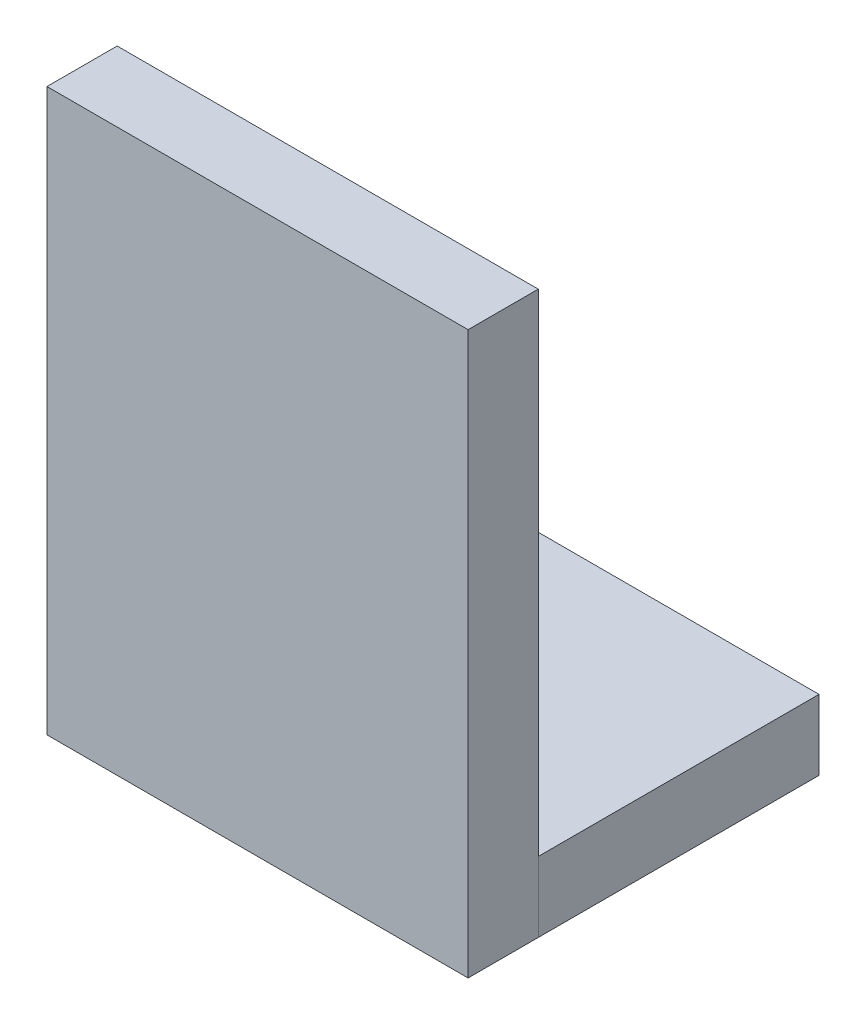
SolidWorks part; units mm, degrees
material "Rubber"
ref_plane "Front Plane" through (0, 0, 0) normal (0, 0, 1) x (1, 0, 0)
ref_plane "Top Plane" through (0, 0, 0) normal (0, 1, 0) x (1, 0, 0)
ref_plane "Right Plane" through (0, 0, 0) normal (1, 0, 0) x (0, 0, -1)
sketch "Sketch1" plane through (0, 0, 0) normal (0, 1, 0) x (1, 0, 0)
  line L1 (0, 0) -> (7.62, 0)
  line L2 (0, 0) -> (0, -5.08)
  line L3 (0, -5.08) -> (7.62, -5.08)
  line L4 (7.62, 0) -> (7.62, -5.08)
  dimension "D1" = 7.62
  dimension "D2" = 5.08
extrude "Boss-Extrude1" add sketch "Sketch1" along normal blind 1.27
sketch "Sketch2" plane through (0, 0, 5.08) normal (0, 0, 1) x (1, 0, 0)
  line L1 (0, 0) -> (7.62, 0)
  line L2 (0, 0) -> (0, 10.16)
  line L3 (0, 10.16) -> (7.62, 10.16)
  line L4 (7.62, 0) -> (7.62, 10.16)
  dimension "D1" = 10.16
extrude "Boss-Extrude2" add sketch "Sketch2" along normal blind 1.27 separate body
